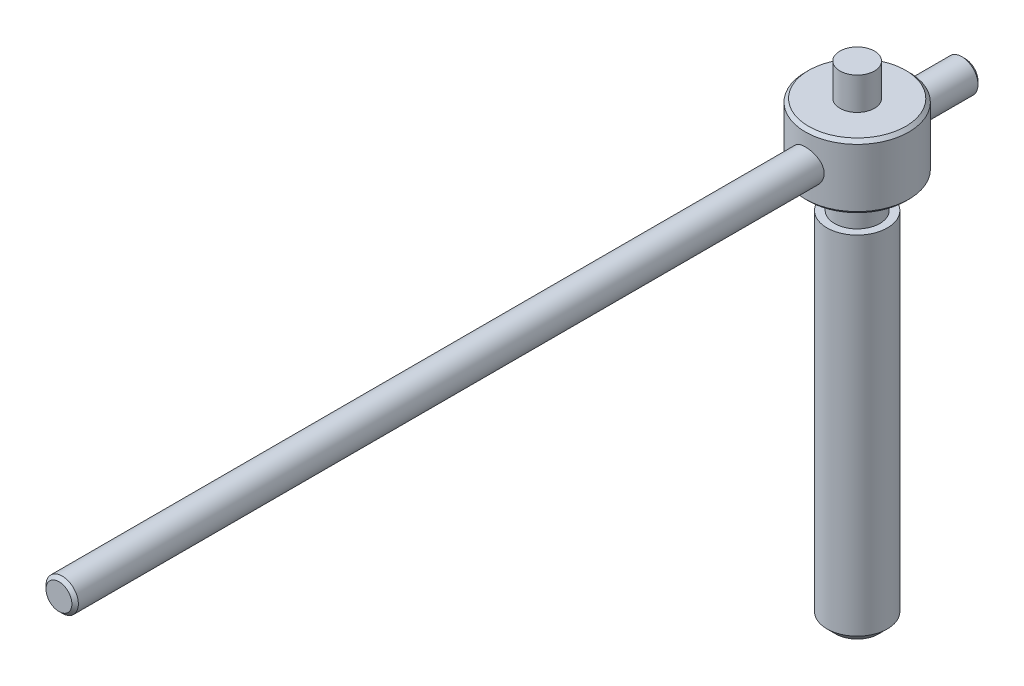
SolidWorks part; units mm, degrees
material "合金钢"
ref_plane "前视基准面" through (0, 0, 0) normal (0, 0, 1) x (1, 0, 0)
ref_plane "上视基准面" through (0, 0, 0) normal (0, 1, 0) x (1, 0, 0)
ref_plane "右视基准面" through (0, 0, 0) normal (1, 0, 0) x (0, 0, -1)
other "Configuration Table"
sketch "草图1" plane through (0, 0, 0) normal (0, 1, 0) x (1, 0, 0)
  circle A0 centre (0, 0) radius 14
  dimension "D1" = 28
extrude "凸台-拉伸1" add sketch "草图1" along normal blind 165
sketch "草图2" plane through (0, 165, 0) normal (0, 1, 0) x (1, 0, 0)
  circle A0 centre (0, 0) radius 10.5
  dimension "D1" = 21
extrude "凸台-拉伸2" add sketch "草图2" along normal blind 15
chamfer "倒角2" distance 4 angle 45 1 edges at (0, 0, 14)
sketch "草图4" plane through (0, 180, 0) normal (0, 1, 0) x (1, 0, 0)
  circle A0 centre (0, 0) radius 24
  dimension "D1" = 48
extrude "凸台-拉伸3" add sketch "草图4" along normal blind 30
sketch "草图5" plane through (0, 210, 0) normal (0, 1, 0) x (1, 0, 0)
  circle A0 centre (0, 0) radius 8
  dimension "D1" = 16
extrude "凸台-拉伸4" add sketch "草图5" along normal blind 15
sketch "草图6" plane through (0, 0, 0) normal (0, 0, 1) x (1, 0, 0)
  line L2 (0, 210) -> (0, 180) construction
  line L3 (24, 210) -> (-24, 210) construction
  line L4 (-10.5, 180) -> (10.5, 180) construction
  circle A0 centre (0, 195) radius 7.5
  point P6 (0, 195)
  dimension "D1" = 15
extrude "凸台-拉伸5" add sketch "草图6" along normal blind 370 and the other way blind 50
chamfer "倒角3" distance 1.5 angle 45 4 edges at (0, 180, 24) (7.5, 195, 370) (7.5, 195, -50) (0, 210, 24)
